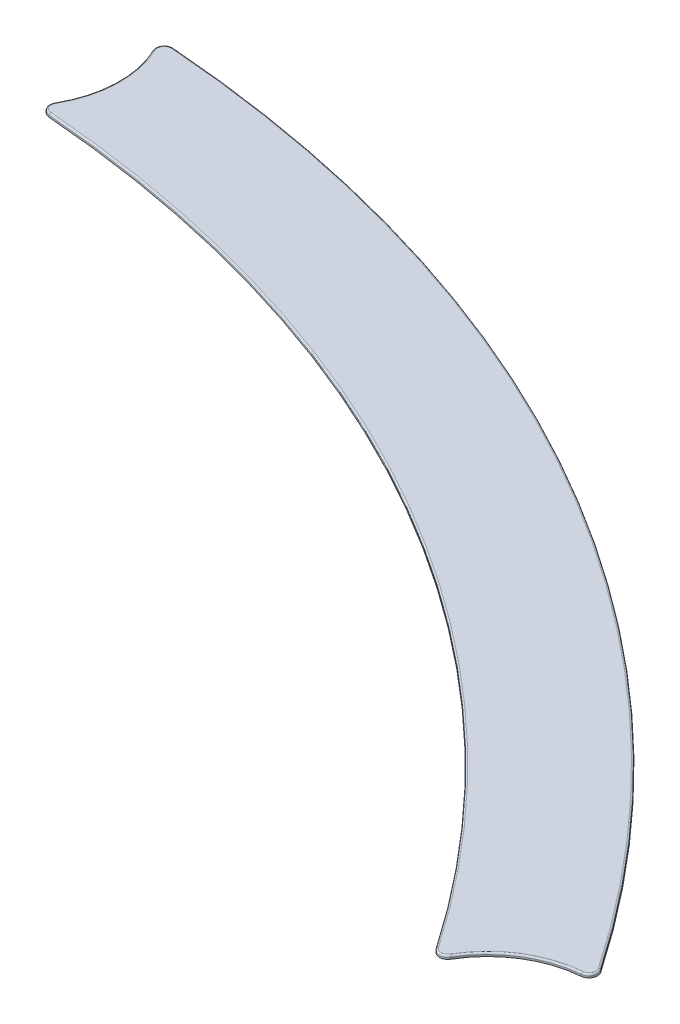
SolidWorks part; units mm, degrees
ref_plane "Front Plane" through (0, 0, 0) normal (0, 0, 1) x (1, 0, 0)
ref_plane "Top Plane" through (0, 0, 0) normal (0, 1, 0) x (1, 0, 0)
ref_plane "Right Plane" through (0, 0, 0) normal (1, 0, 0) x (0, 0, -1)
sketch "Sketch1" plane through (0, 0, 0) normal (0, 1, 0) x (1, 0, 0)
  line L0 (0, 0) -> (0, 75.5) construction
  line L1 (0, 0) -> (65.3849, 37.75) construction
  line L2 (20.6559, 67.9289) -> (20.9469, 68.8856) construction
  line L3 (22.9834, 75.5828) -> (23.2743, 76.5396) construction
  circle A0 centre (0, 0) radius 71 construction
  circle A1 centre (0, 0) radius 80 construction
  arc A2 (65.7885, 43.7364) -> (59.8394, 40.0406) centre (65.3849, 37.75) ccw
  arc A3 (65.7885, 43.7364) -> (4.9826, 78.8427) centre (0, 0) ccw
  arc A4 (4.7565, 71.8427) -> (4.9826, 78.8427) centre (0, 75.5) ccw
  arc A6 (59.8394, 40.0406) -> (4.7565, 71.8427) centre (0, 0) ccw
  dimension "D1" = 160
  dimension "D2" = 142
  dimension "D5" = 6
  dimension "D3" = 60
  dimension "D4" = 75.5
  dimension "D6" = 7
extrude "Boss-Extrude1" add sketch "Sketch1" along normal blind 0.2
fillet "Fillet1" radius 0.5 4 edges at (4.7565, 0.1, -71.8427) (4.9826, 0.1, -78.8427) (59.8394, 0.1, -40.0406) (65.7885, 0.1, -43.7364)
fillet "Fillet2" radius 0.1 8 edges at (5.4635, 0.2, -78.5629) (39.5, 0.2, -68.416) (65.3057, 0.2, -44.013) (62.1886, 0.2, -42.8278) (59.7912, 0.2, -40.53) (36, 0.2, -62.3538) (5.2045, 0.2, -72.0457) (5.9956, 0.2, -75.2708)
